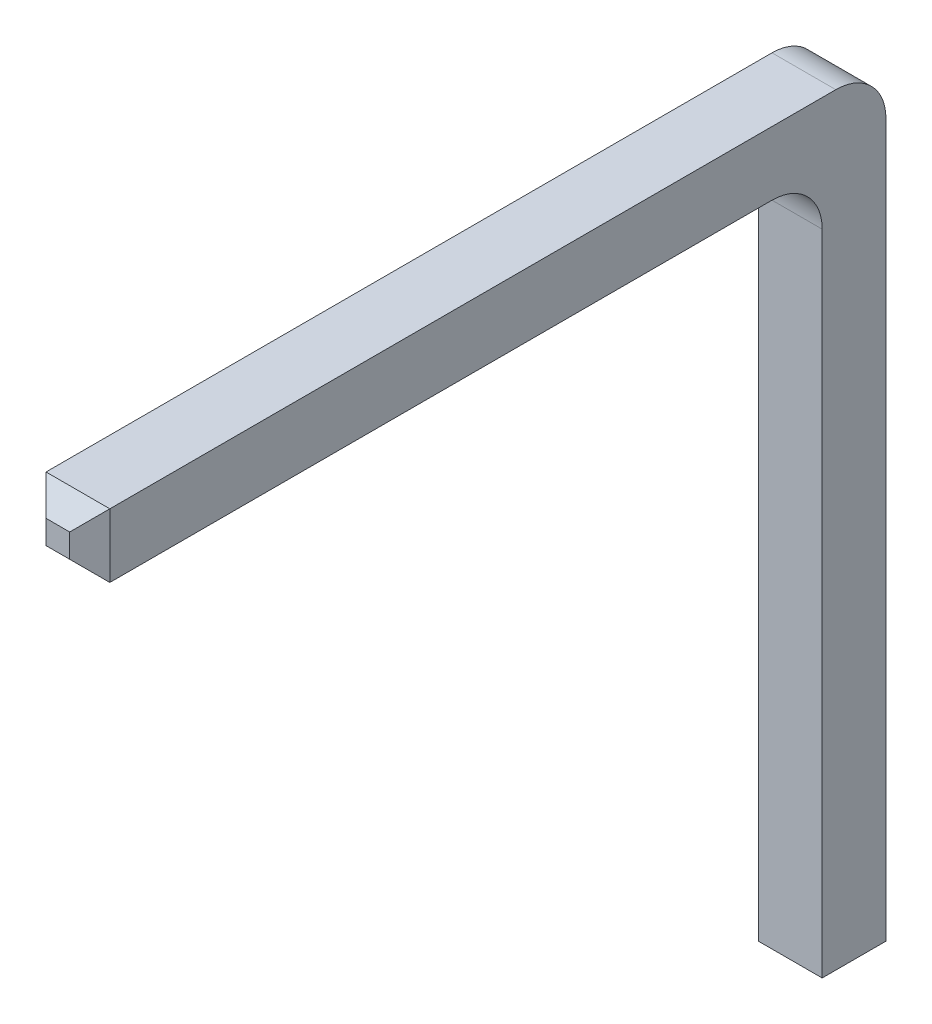
SolidWorks part; units mm, degrees
ref_plane "Alzado" through (0, 0, 0) normal (0, 0, 1) x (1, 0, 0)
ref_plane "Planta" through (0, 0, 0) normal (0, 1, 0) x (1, 0, 0)
ref_plane "Vista lateral" through (0, 0, 0) normal (1, 0, 0) x (0, 0, -1)
sketch "Croquis1" plane through (0, 0, 0) normal (0, 1, 0) x (1, 0, 0)
  line L1 (0, 0) -> (0.636, 0)
  line L2 (0, 0) -> (0, -0.636)
  line L3 (0, -0.636) -> (0.636, -0.636)
  line L4 (0.636, 0) -> (0.636, -0.636)
extrude "Saliente-Extruir1" add sketch "Croquis1" along normal blind 7.8
sketch "Croquis2" plane through (0, 0, 0.636) normal (0, 0, 1) x (1, 0, 0)
  line L0 (0.636, 7.8) -> (0.636, 0) construction
  line L1 (0, 7.8) -> (0.636, 7.8)
  line L2 (0, 7.8) -> (0, 7.164)
  line L3 (0, 7.164) -> (0.636, 7.164)
  line L4 (0.636, 7.8) -> (0.636, 7.164)
extrude "Saliente-Extruir2" add sketch "Croquis2" along normal blind 7.3
fillet "Redondeo1" radius 0.5 2 edges at (0.318, 7.8, 0)
chamfer "Chaflán1" distance 0.2 angle 45 4 edges at (0.636, 7.482, 7.936) (0.318, 7.8, 7.936) (0, 7.482, 7.936) (0.318, 7.164, 7.936)
chamfer "Chaflán2" distance 0.2 angle 45 4 edges at (0, 0, 0.318) (0.318, 0, 0) (0.636, 0, 0.318) (0.318, 0, 0.636)
